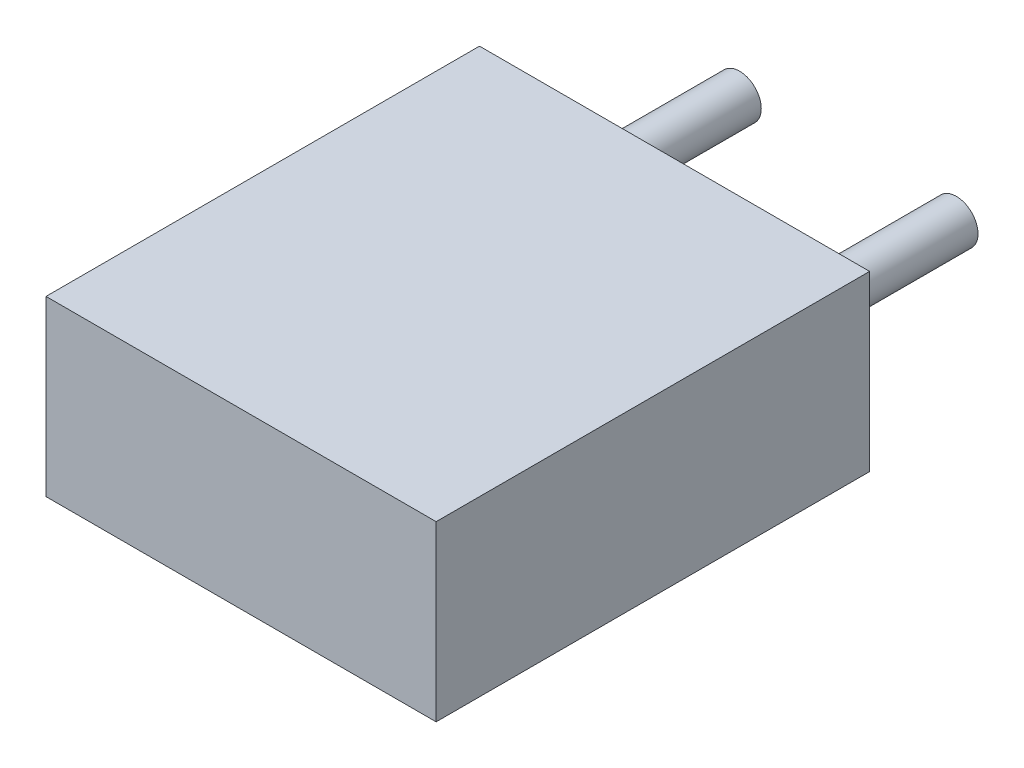
SolidWorks part; units mm, degrees
ref_plane "Front Plane" through (0, 0, 0) normal (0, 0, 1) x (1, 0, 0)
ref_plane "Top Plane" through (0, 0, 0) normal (0, 1, 0) x (1, 0, 0)
ref_plane "Right Plane" through (0, 0, 0) normal (1, 0, 0) x (0, 0, -1)
sketch "Sketch1" plane through (0, 0, 0) normal (0, 0, 1) x (1, 0, 0)
  line L0 (-1, 1) -> (-1, -1)
  line L1 (-1, -1) -> (3.5, -1)
  line L2 (3.5, -1) -> (3.5, 1)
  line L3 (3.5, 1) -> (-1, 1)
extrude "Component_Outline" add sketch "Sketch1" along normal blind 5 separate body
sketch "Sketch2" plane through (0, 0, 0) normal (0, 0, 1) x (1, 0, 0)
  circle A0 centre (0, 0) radius 0.25
extrude "1" add sketch "Sketch2" against normal blind 2 separate body
sketch "Sketch3" plane through (0, 0, 0) normal (0, 0, 1) x (1, 0, 0)
  circle A0 centre (2.5, 0) radius 0.25
extrude "2" add sketch "Sketch3" against normal blind 2 separate body
sketch3d "3DSketch1"
  line L0 (0, 0, 0) -> (1, 0, 0)
  line L1 (0, 0, 0) -> (0, 1, 0)
  line L2 (0, 0, 0) -> (0, 0, 1)
  point P0 (0, 0, 0)
